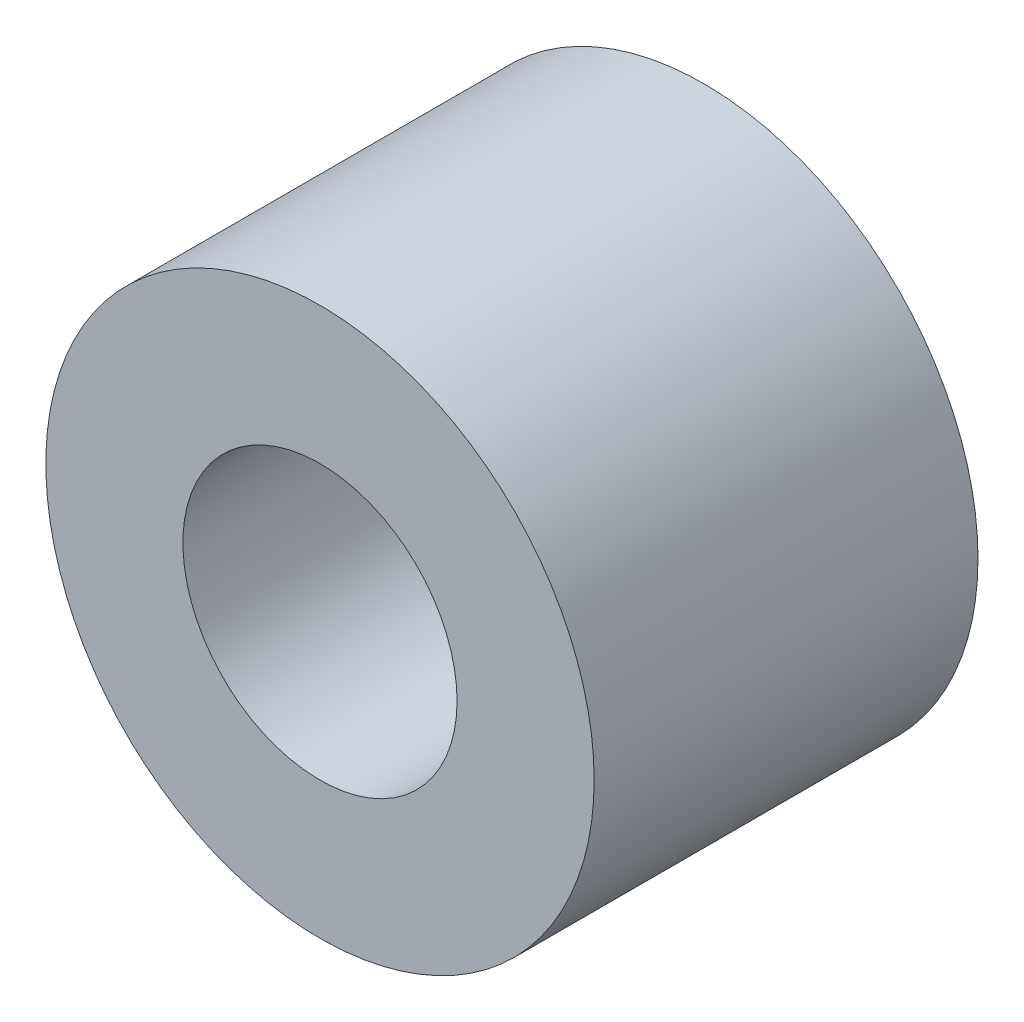
SolidWorks part; units mm, degrees
ref_plane "Front Plane" through (0, 0, 0) normal (0, 0, 1) x (1, 0, 0)
ref_plane "Top Plane" through (0, 0, 0) normal (0, 1, 0) x (1, 0, 0)
ref_plane "Right Plane" through (0, 0, 0) normal (1, 0, 0) x (0, 0, -1)
sketch "Sketch1" plane through (0, 0, 0) normal (0, 0, 1) x (1, 0, 0)
  circle A0 centre (0, 0) radius 5
  dimension "D1" = 10
extrude "Boss-Extrude1" add sketch "Sketch1" along normal blind 7
hole_wizard "Ø5.0mm Dowel Hole1" positions "Sketch2" profile "Sketch3" hole size "Ø5.0" standard "ANSI Metric" end condition up to next
sketch "Sketch2" plane through (0, 0, 7) normal (0, 0, 1) x (1, 0, 0)
  point P0 (0, 0)
sketch "Sketch3" plane through (0, 0, 7) normal (1, 0, 0) x (0, -1, 0)
  line L0 (0, 0) -> (0, 7)
  line L1 (0, 7) -> (2.5, 7)
  line L2 (2.5, 7) -> (2.5, 0)
  line L5 (2.5, 0) -> (0, 0)
  line L11 (0, -6.35) -> (0, 107.95) construction
  dimension "Thru Hole Dia." = 5
  dimension "Thru Hole Depth" = 7
equation "\"Length\"=7"
equation "\"D1@Boss-Extrude1\"=\"Length\""
